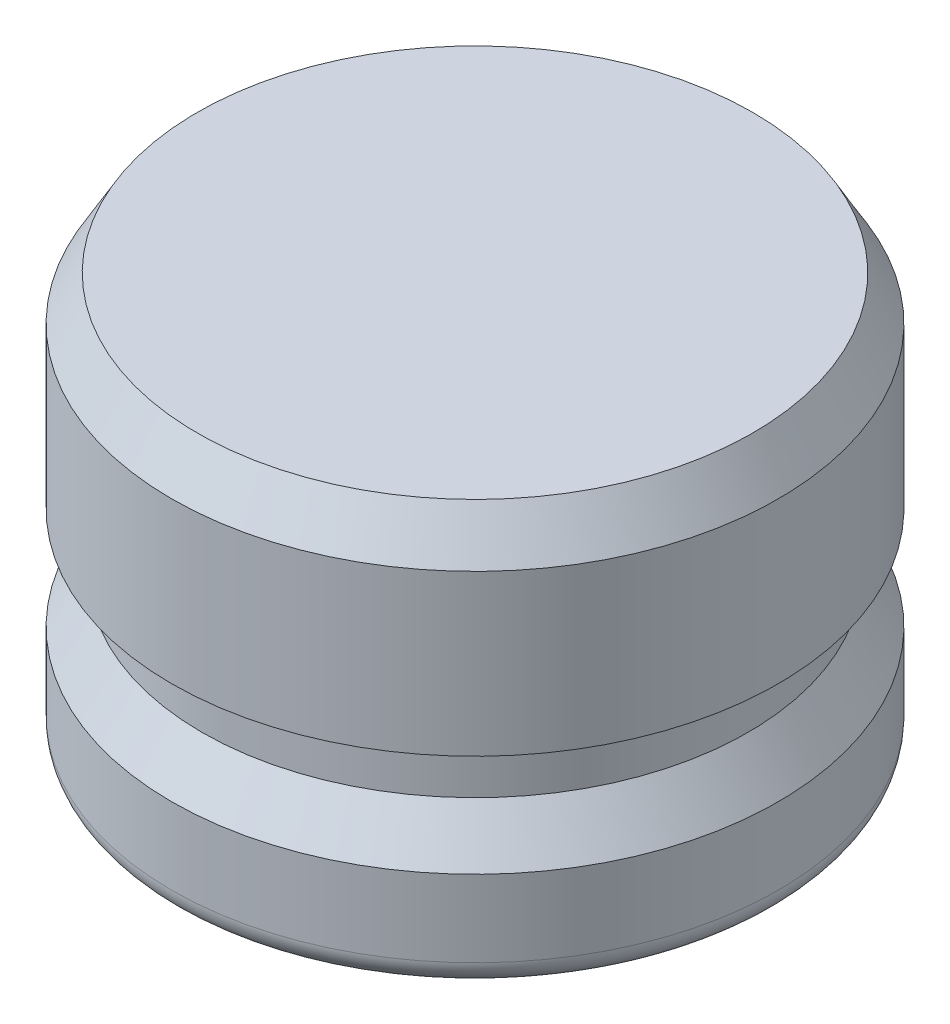
SolidWorks part; units mm, degrees
ref_plane "Front Plane" through (0, 0, 0) normal (0, 0, 1) x (1, 0, 0)
ref_plane "Top Plane" through (0, 0, 0) normal (0, 1, 0) x (1, 0, 0)
ref_plane "Right Plane" through (0, 0, 0) normal (1, 0, 0) x (0, 0, -1)
sketch "Sketch1" plane through (0, 0, 0) normal (0, 0, 1) x (1, 0, 0)
  line L0 (0, 0) -> (0, 12.7) construction
  line L1 (0, 0) -> (-9.4234, 0)
  line L2 (-9.4234, 0) -> (-9.4234, 3.175)
  line L4 (-8.4836, 4.572) -> (-8.4836, 6.35)
  line L5 (-8.4836, 6.35) -> (-9.4234, 6.35)
  line L6 (-9.4234, 6.35) -> (-9.4234, 12.7)
  line L7 (-9.4234, 12.7) -> (0, 12.7)
  line L8 (-9.525, 16.6801) -> (-9.525, -9.6051) construction
  line L9 (0, 0) -> (0, 12.7)
  line L10 (-8.4836, 4.572) -> (-9.4234, 3.175)
  dimension "D1" = 12.7
  dimension "D2" = 9.4234
  dimension "D3" = 1.778
  dimension "D4" = 3.175
  dimension "D5" = 9.525
  dimension "D6" = 8.4836
  dimension "D7" = 6.35
revolve "Revolve1" add sketch "Sketch1" angle 360 about L9
fillet "Fillet1" radius 0.7937 1 edges at (0, 0, -9.4234)
chamfer "Chamfer1" distance 0.7937 angle 60 1 edges at (0, 12.7, -9.4234)
